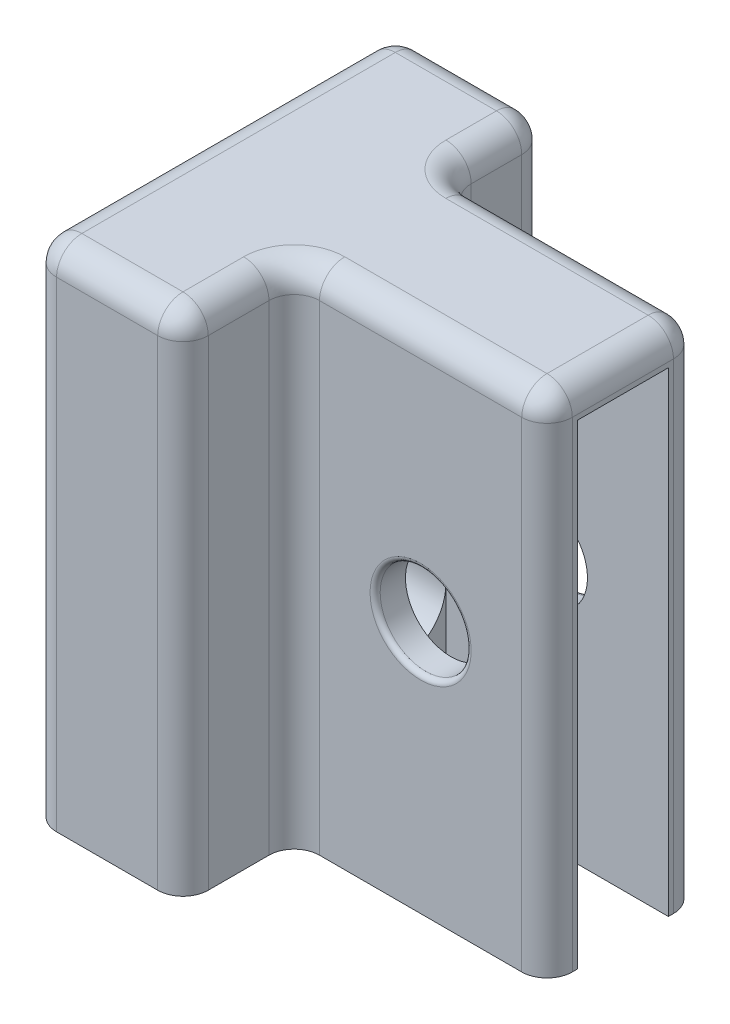
SolidWorks part; units mm, degrees
ref_plane "Front Plane" through (0, 0, 0) normal (0, 0, 1) x (1, 0, 0)
ref_plane "Top Plane" through (0, 0, 0) normal (0, 1, 0) x (1, 0, 0)
ref_plane "Right Plane" through (0, 0, 0) normal (1, 0, 0) x (0, 0, -1)
sketch "Sketch1" plane through (0, 0, 0) normal (0, 1, 0) x (1, 0, 0)
  line L0 (24, 72) -> (30, 72)
  line L1 (0, 0) -> (30, 0)
  line L2 (0, 0) -> (0, 72)
  line L3 (0, 72) -> (6, 72)
  line L4 (30, 0) -> (30, 72)
  line L9 (6, 72) -> (24, 72)
  dimension "D1" = 30
  dimension "D2" = 72
extrude "Boss-Extrude1" add sketch "Sketch1" along normal blind 100
sketch "Sketch2" plane through (30, 0, 0) normal (1, 0, 0) x (0, 0, -1)
  line L7 (0, 100) -> (72, 100) construction
  line L8 (22, 100) -> (52, 100)
  line L9 (22, 100) -> (22, 0)
  line L10 (22, 0) -> (52, 0)
  line L11 (52, 100) -> (52, 0)
  line L12 (0, 0) -> (72, 0) construction
  line L13 (0, 100) -> (0, 0) construction
  dimension "D1" = 30
  dimension "D2" = 22
extrude "Boss-Extrude3" add sketch "Sketch2" along normal blind 50
sketch "Sketch6" plane through (80, 0, 0) normal (1, 0, 0) x (0, 0, -1)
  line L0 (22, 0) -> (52, 0) construction
  line L1 (28, 94) -> (46, 94)
  line L2 (28, 94) -> (28, 0)
  line L3 (28, 0) -> (46, 0)
  line L4 (46, 94) -> (46, 0)
  line L5 (22, 100) -> (22, 0) construction
  line L6 (52, 0) -> (52, 100) construction
  line L7 (52, 100) -> (22, 100) construction
  dimension "D1" = 6
  dimension "D2" = 6
  dimension "D3" = 6
extrude "Cut-Extrude1" cut sketch "Sketch6" against normal blind 44
sketch "Sketch7" plane through (0, 0, 0) normal (0, -1, 0) x (1, 0, 0)
  line L0 (6, -6) -> (6, -66)
  line L1 (6, -66) -> (24, -66)
  line L2 (24, -6) -> (24, -66)
  line L3 (6, -6) -> (24, -6)
  line L4 (30, 0) -> (30, -22) construction
  line L5 (0, 0) -> (30, 0) construction
  dimension "D1" = 6
  dimension "D2" = 18
  dimension "D3" = 60
  dimension "D4" = 6
extrude "Cut-Extrude2" cut sketch "Sketch7" against normal blind 94
sketch "Sketch8" plane through (0, 0, 0) normal (-1, 0, 0) x (0, 0, 1)
  line L0 (-72, 100) -> (-72, 0) construction
  line L1 (-66, 0) -> (-6, 0) construction
  circle A0 centre (-37, 35) radius 9
  dimension "D1" = 35
  dimension "D2" = 18
  dimension "D3" = 35
extrude "Cut-Extrude3" cut sketch "Sketch8" against normal through all both and the other way through all
fillet "Fillet1" radius 5 16 edges at (80, 50, -52) (80, 50, -22) (15, 100, -72) (30, 100, -62) (55, 100, -52) (80, 100, -37) (55, 100, -22) (30, 50, -22) (30, 100, -11) (0, 100, -36) (0, 50, 0) (15, 100, 0) (30, 50, 0) (0, 50, -72) (30, 50, -72) (30, 50, -52)
sketch "Sketch9" plane through (0, 0, -22) normal (0, 0, 1) x (1, 0, 0)
  line L0 (75, 0) -> (75, 95) construction
  line L1 (75, 95) -> (35, 95) construction
  circle A0 centre (55, 50) radius 9
  dimension "D1" = 20
  dimension "D3" = 18
  dimension "D2" = 45
extrude "Cut-Extrude4" cut sketch "Sketch9" against normal through all
fillet "Fillet2" radius 1 3 edges at (0, 35, -46) (64, 50, -52) (64, 50, -22)
